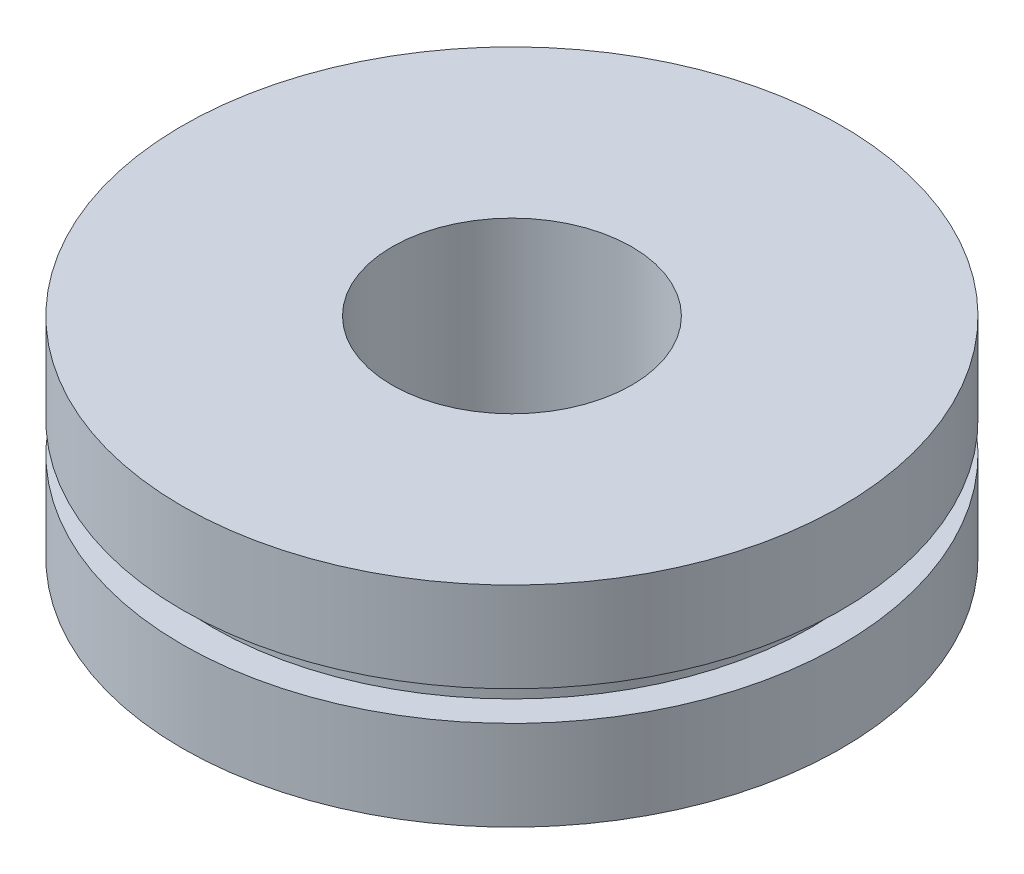
SolidWorks part; units mm, degrees
ref_plane "前视基准面" through (0, 0, 0) normal (0, 0, 1) x (1, 0, 0)
ref_plane "上视基准面" through (0, 0, 0) normal (0, 1, 0) x (1, 0, 0)
ref_plane "右视基准面" through (0, 0, 0) normal (1, 0, 0) x (0, 0, -1)
sketch "草图1" plane through (0, 0, 0) normal (0, 1, 0) x (1, 0, 0)
  circle A0 centre (0, 0) radius 4
  circle A1 centre (0, 0) radius 11
  dimension "D1" = 8
  dimension "D2" = 22
extrude "凸台-拉伸1" add sketch "草图1" along normal blind 7
ref_plane "基准面1" through (0, 3.5, 0) normal (0, 1, 0) x (1, 0, 0)
sketch "草图2" plane through (0, 3.5, 0) normal (0, 1, 0) x (1, 0, 0)
  circle A0 centre (0, 0) radius 10
  circle A1 centre (0, 0) radius 12
  dimension "D1" = 0
extrude "切除-拉伸1" cut sketch "草图2" against normal blind 0.5 and the other way blind 0.5
